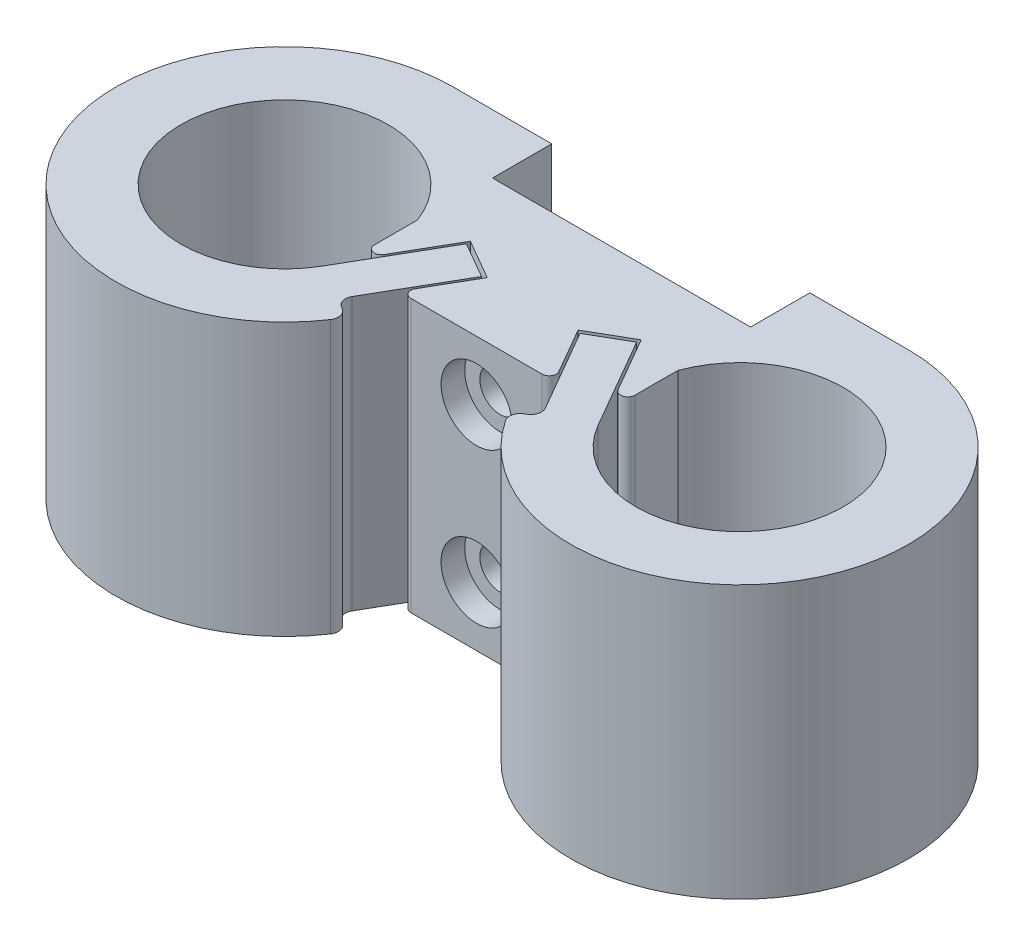
SolidWorks part; units mm, degrees
ref_plane "Front Plane" through (0, 0, 0) normal (0, 0, 1) x (1, 0, 0)
ref_plane "Top Plane" through (0, 0, 0) normal (0, 1, 0) x (1, 0, 0)
ref_plane "Right Plane" through (0, 0, 0) normal (1, 0, 0) x (0, 0, -1)
sketch "Sketch1" plane through (0, 0, 0) normal (0, 1, 0) x (1, 0, 0)
  line L1 (-11, 3) -> (11, 3)
  line L2 (-11, 3) -> (-11, -3)
  line L3 (-11, -3) -> (11, -3)
  line L4 (11, 3) -> (11, -3)
  line L5 (-11, 3) -> (11, -3) construction
  line L6 (-11, -3) -> (11, 3) construction
  point P4 (0, 0)
  dimension "D1" = 6
  dimension "D2" = 22
extrude "Boss-Extrude1" add sketch "Sketch1" along normal blind 23
sketch "Sketch2" plane through (0, 23, 0) normal (0, 1, 0) x (1, 0, 0)
  line L0 (-19.2196, 0) -> (0, 0) construction
  line L1 (0, 0) -> (0, 3) construction
  line L2 (11, 3) -> (-11, 3) construction
  line L3 (-11, 3) -> (-7.3427, 3)
  line L4 (-11.6419, -4.375) -> (-8.6108, -6.125)
  line L5 (-19.2196, 0) -> (-11.6419, -4.375) construction
  line L6 (19.2196, 0) -> (11.6419, -4.375) construction
  line L7 (11.6419, -4.375) -> (8.6108, -6.125)
  line L8 (11, 3) -> (7.3427, 3)
  arc A0 (-11, 3) -> (-11.6419, -4.375) centre (-19.2196, 0) ccw
  arc A2 (-7.3427, 3) -> (-8.6108, -6.125) centre (-19.2196, 0) ccw
  arc A4 (-8.6108, -6.125) -> (-6.9696, 0) centre (-19.2196, 0) ccw construction
  arc A5 (-11.6419, -4.375) -> (-10.4696, 0) centre (-19.2196, 0) ccw construction
  arc A6 (-10.4696, 0) -> (-11, 3) centre (-19.2196, 0) ccw construction
  arc A7 (-6.9696, 0) -> (-7.3427, 3) centre (-19.2196, 0) ccw construction
  arc A8 (6.9696, 0) -> (7.3427, 3) centre (19.2196, 0) cw construction
  arc A9 (10.4696, 0) -> (11, 3) centre (19.2196, 0) cw construction
  arc A10 (11.6419, -4.375) -> (10.4696, 0) centre (19.2196, 0) cw construction
  arc A11 (8.6108, -6.125) -> (6.9696, 0) centre (19.2196, 0) cw construction
  arc A12 (7.3427, 3) -> (8.6108, -6.125) centre (19.2196, 0) cw
  arc A13 (11, 3) -> (11.6419, -4.375) centre (19.2196, 0) cw
  dimension "D1" = 17.5
  dimension "D2" = 3.5
  dimension "D3" = 30
extrude "Boss-Extrude2" add sketch "Sketch2" against normal up to surface (23 mm away) up to face at (0, 0, 0)
sketch "Sketch3" plane through (0, 23, 0) normal (0, 1, 0) x (1, 0, 0)
  line L0 (-19.2196, 12.25) -> (19.2196, 12.25)
  line L1 (-7.3427, 3) -> (7.3427, 3)
  arc A0 (-7.3427, 3) -> (-8.6108, -6.125) centre (-19.2196, 0) ccw construction
  arc A1 (8.6108, -6.125) -> (7.3427, 3) centre (19.2196, 0) ccw construction
  arc A2 (-7.3427, 3) -> (-19.2196, 12.25) centre (-19.2196, 0) ccw
  arc A3 (7.3427, 3) -> (19.2196, 12.25) centre (19.2196, 0) cw
  arc A4 (8.6108, -6.125) -> (7.3427, 3) centre (19.2196, 0) ccw construction
extrude "Boss-Extrude3" add sketch "Sketch3" against normal up to surface (23 mm away) up to face at (0, 0, 0.561)
sketch "Sketch8" plane through (0, 0, 0) normal (0, -1, 0) x (1, 0, 0)
  line L0 (11.6419, 4.375) -> (7.1419, -3.4192) construction
  line L1 (7.1419, -3.4192) -> (4.1108, -1.6692) construction
  line L2 (4.1108, -1.6692) -> (8.6108, 6.125) construction
  line L3 (8.6108, 6.125) -> (11.6419, 4.375) construction
  line L4 (11, 2.8632) -> (7.2151, -3.6924)
  line L5 (11, 3) -> (11, -3) construction
  line L6 (7.2151, -3.6924) -> (3.8376, -1.7424)
  line L7 (3.8376, -1.7424) -> (6.5757, 3)
  line L8 (-11, 3) -> (11, 3) construction
  line L9 (0, -18.0645) -> (0, 0) construction
  line L10 (6.5757, 3) -> (11, 3)
  line L11 (11, 3) -> (11, 2.8632)
  line L12 (-6.5757, 3) -> (-11, 3)
  line L13 (-3.8376, -1.7424) -> (-6.5757, 3)
  line L14 (-7.2151, -3.6924) -> (-3.8376, -1.7424)
  line L15 (-11, 2.8632) -> (-7.2151, -3.6924)
  line L16 (-11, 3) -> (-11, 2.8632)
  dimension "D1" = 9
  dimension "D2" = 0.2
  dimension "D3" = 0.2
  dimension "D4" = 0.2
extrude "Cut-Extrude1" cut sketch "Sketch8" against normal through all
sketch "Sketch5" plane through (0, 23, 0) normal (0, 1, 0) x (1, 0, 0)
  line L0 (19.2196, 12.25) -> (-19.2196, 12.25) construction
  line L1 (-10, 12.25) -> (10, 12.25)
  line L2 (-10, 12.25) -> (-10, 14.25)
  line L3 (-10, 14.25) -> (10, 14.25)
  line L4 (10, 12.25) -> (10, 14.25)
  line L5 (-10, 12.25) -> (10, 14.25) construction
  line L6 (-10, 14.25) -> (10, 12.25) construction
  point P4 (0, 13.25)
  dimension "D1" = 2
  dimension "D2" = 20
extrude "Boss-Extrude4" add sketch "Sketch5" against normal blind 45
sketch "Sketch6" plane through (-10, 0, 0) normal (-1, 0, 0) x (0, 0, 1)
  line L0 (-12.25, 0) -> (12.25, 0) construction
  line L1 (-12.25, -22) -> (-11.25, -22)
  line L2 (-12.25, -22) -> (-12.25, -20)
  line L3 (-12.25, -20) -> (-11.25, -20)
  line L4 (-11.25, -22) -> (-11.25, -20)
  line L5 (-12.25, -22) -> (-11.25, -20) construction
  line L6 (-12.25, -20) -> (-11.25, -22) construction
  line L7 (-11.25, -22) -> (-9.25, -22)
  line L8 (-11.25, -22) -> (-11.25, -1)
  line L9 (-11.25, -1) -> (-9.25, -1)
  line L10 (-9.25, -22) -> (-9.25, -1)
  line L11 (-11.25, -22) -> (-9.25, -1) construction
  line L12 (-11.25, -1) -> (-9.25, -22) construction
  point P4 (-11.75, -21)
  point P9 (-10.25, -11.5)
  line M12 (-12.25, -22) -> (-12.25, 0)
  dimension "D1" = 2
  dimension "D2" = 1
  dimension "D3" = 1
  dimension "D4" = 2
extrude "Boss-Extrude5" add sketch "Sketch6" against normal up to surface (20 mm away) contours L1 L4 L3 M12 | L7 L10 L9 L8 L4 up to face at (10, 0.4, -13.05)
sketch "Sketch7" plane through (0, 23, 0) normal (0, 1, 0) x (1, 0, 0)
  line L0 (10, 14.25) -> (19.2196, 14.25)
  line L1 (10, 14.25) -> (-10, 14.25) construction
  line L2 (10, 12.25) -> (19.2196, 12.25)
  line L3 (10, 14.25) -> (10, 12.25)
  line L4 (8.6108, -6.125) -> (6.8788, -7.125)
  line L5 (11.6419, -4.375) -> (8.6108, -6.125) construction
  line L6 (0, 0) -> (0, 14.25) construction
  line L7 (-8.6108, -6.125) -> (-6.8788, -7.125)
  line L8 (-10, 14.25) -> (-19.2196, 14.25)
  line L9 (-10, 14.25) -> (-10, 12.25)
  line L10 (-10, 12.25) -> (-19.2196, 12.25)
  arc A0 (6.8788, -7.125) -> (19.2196, 14.25) centre (19.2196, 0) ccw
  arc A1 (8.6108, -6.125) -> (19.2196, 12.25) centre (19.2196, 0) ccw
  arc A2 (8.6108, -6.125) -> (19.2196, 12.25) centre (19.2196, 0) ccw construction
  arc A3 (10, 10.8656) -> (6.8788, -7.125) centre (19.2196, 0) ccw construction
  arc A4 (19.2196, 14.25) -> (10, 10.8656) centre (19.2196, 0) ccw construction
  arc A5 (19.2196, 12.25) -> (8.6108, -6.125) centre (19.2196, 0) ccw construction
  arc A6 (-6.8788, -7.125) -> (-19.2196, 14.25) centre (-19.2196, 0) cw
  arc A7 (-8.6108, -6.125) -> (-19.2196, 12.25) centre (-19.2196, 0) cw
sketch "Sketch9" plane through (0, 0, 0) normal (0, -1, 0) x (1, 0, 0)
  line L0 (11.6419, 4.375) -> (7.1919, -3.3326)
  line L1 (7.1919, -3.3326) -> (4.1608, -1.5826)
  line L2 (4.1608, -1.5826) -> (8.6108, 6.125)
  line L3 (0, 0) -> (0, -19.6034) construction
  line L4 (8.6108, 6.125) -> (11.6419, 4.375) construction
  line L5 (3.8376, -1.7424) -> (7.2151, -3.6924) construction
  line L6 (11.6419, 4.375) -> (8.6108, 6.125)
  line L7 (-11.6419, 4.375) -> (-7.1919, -3.3326)
  line L8 (-7.1919, -3.3326) -> (-4.1608, -1.5826)
  line L9 (-4.1608, -1.5826) -> (-8.6108, 6.125)
  line L10 (-11.6419, 4.375) -> (-8.6108, 6.125)
  line M11 (8.6108, 6.125) -> (11.6419, 4.375)
  line M23 (-11.6419, 4.375) -> (-8.6108, 6.125)
  dimension "D1" = 0.3
extrude "Boss-Extrude6" add sketch "Sketch9" against normal up to surface (23 mm away) contours L2 L1 L0 M11 | L8 L9 L7 M23 up to face at (0, 23, -2.308)
fillet "Fillet1" radius 0.6 4 edges at (-11, 11.5, 2.8632) (-6.5757, 11.5, 3) (6.5757, 11.5, 3) (11, 11.5, 2.8632)
extrude "Boss-Extrude7" add sketch "Sketch7" against normal up to surface (23 mm away) up to face at (0, 0, -0.9524)
fillet "Fillet2" radius 0.9 8 edges at (0, -22, -14.25) (0, -22, -9.25) (-10, 0, -13.25) (10, 0, -13.25) (6.8788, 11.5, 7.125) (-6.8788, 11.5, 7.125) (-8.6108, 11.5, 6.125) (8.6108, 11.5, 6.125)
sketch "Sketch10" plane through (0, 0, 0) normal (0, -1, 0) x (1, 0, 0)
  line L1 (10.9, -14.25) -> (-10.9, -14.25)
  line L2 (10.9, -14.25) -> (10.9, -9.25)
  line L3 (10.9, -9.25) -> (-10.9, -9.25)
  line L4 (-10.9, -14.25) -> (-10.9, -9.25)
  line L5 (10.9, -14.25) -> (-10.9, -9.25) construction
  line L6 (10.9, -9.25) -> (-10.9, -14.25) construction
  line L7 (10, -9.25) -> (-10, -9.25) construction
  point P4 (0, -11.75)
  point P6 (0, 0)
extrude "Cut-Extrude2" cut sketch "Sketch10" along normal through all and the other way through all
sketch "Sketch11" plane through (0, 0, 3) normal (0, 0, 1) x (1, 0, 0)
  line L0 (0, 0) -> (0, 23) construction
  line L1 (-5.5364, 0) -> (5.5364, 0) construction
  line L2 (-5.5364, 23) -> (5.5364, 23) construction
  line L3 (0, 11.5) -> (-4.9138, 11.5) construction
  circle A0 centre (0, 5) radius 1.725
  circle A2 centre (0, 18) radius 1.725
  point P8 (0, 4.6663)
  dimension "D2" = 3.45
  dimension "D1" = 5
extrude "Cut-Extrude3" cut sketch "Sketch11" against normal through all
sketch "Sketch12" plane through (0, 0, 3) normal (0, 0, 1) x (1, 0, 0)
  circle A0 centre (0, 5) radius 3
  circle A1 centre (0, 18) radius 3
  dimension "D1" = 6
extrude "Cut-Extrude4" cut sketch "Sketch12" against normal blind 2
